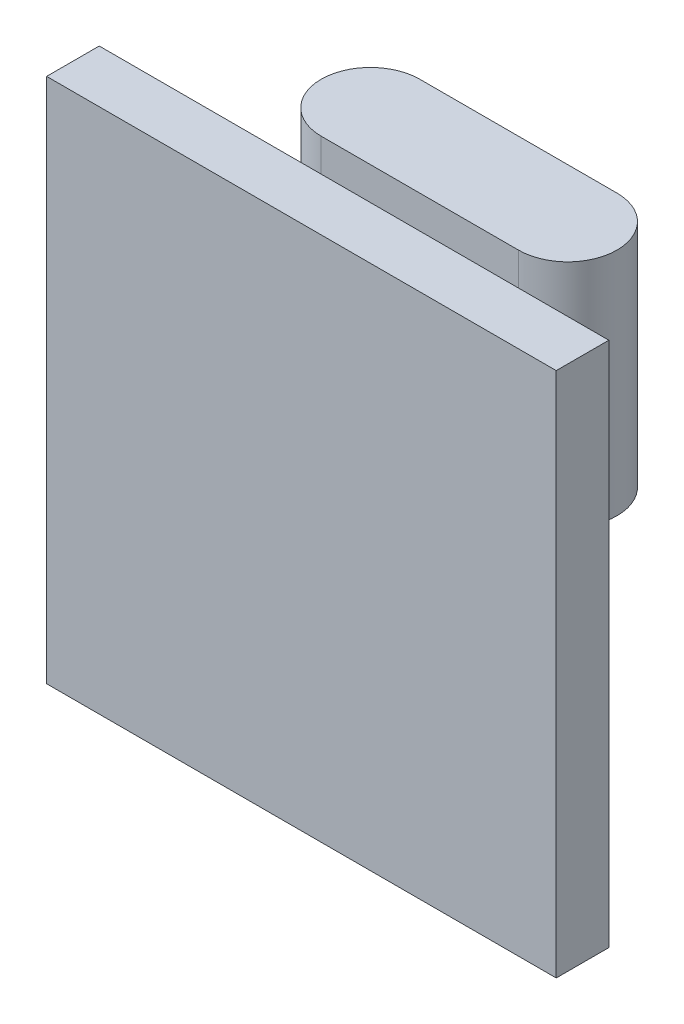
SolidWorks part; units mm, degrees
ref_plane "Plano frontal" through (0, 0, 0) normal (0, 0, 1) x (1, 0, 0)
ref_plane "Plano superior" through (0, 0, 0) normal (0, 1, 0) x (1, 0, 0)
ref_plane "Plano direito" through (0, 0, 0) normal (1, 0, 0) x (0, 0, -1)
sketch "Esboço1" plane through (0, 0, 0) normal (0, 0, 1) x (1, 0, 0)
  line L1 (-7.75, 8) -> (7.75, 8)
  line L2 (-7.75, 8) -> (-7.75, -8)
  line L3 (-7.75, -8) -> (7.75, -8)
  line L4 (7.75, 8) -> (7.75, -8)
  line L5 (-7.75, 8) -> (7.75, -8) construction
  line L6 (-7.75, -8) -> (7.75, 8) construction
  point P0 (0, 0)
  dimension "D1" = 16
  dimension "D2" = 15.5
extrude "Ressalto-extrusão1" add sketch "Esboço1" along normal blind 1.6
sketch "Esboço3" plane through (0, 8, 0) normal (0, 1, 0) x (1, 0, 0)
  line L0 (-1, 1.5) -> (5, 1.5) construction
  line L1 (-1, 3) -> (5, 3)
  line L2 (-1, 0) -> (5, 0)
  line L3 (-7.75, 0) -> (7.75, 0) construction
  arc A0 (-1, 3) -> (-1, 0) centre (-1, 1.5) ccw
  arc A1 (5, 0) -> (5, 3) centre (5, 1.5) ccw
  point P2 (2, 1.5)
  point P9 (1.475, 1.5)
  dimension "D1" = 9
  dimension "D2" = 1.5
  dimension "D3" = 2
extrude "Ressalto-extrusão2" add sketch "Esboço3" along normal blind 1 and the other way blind 6
